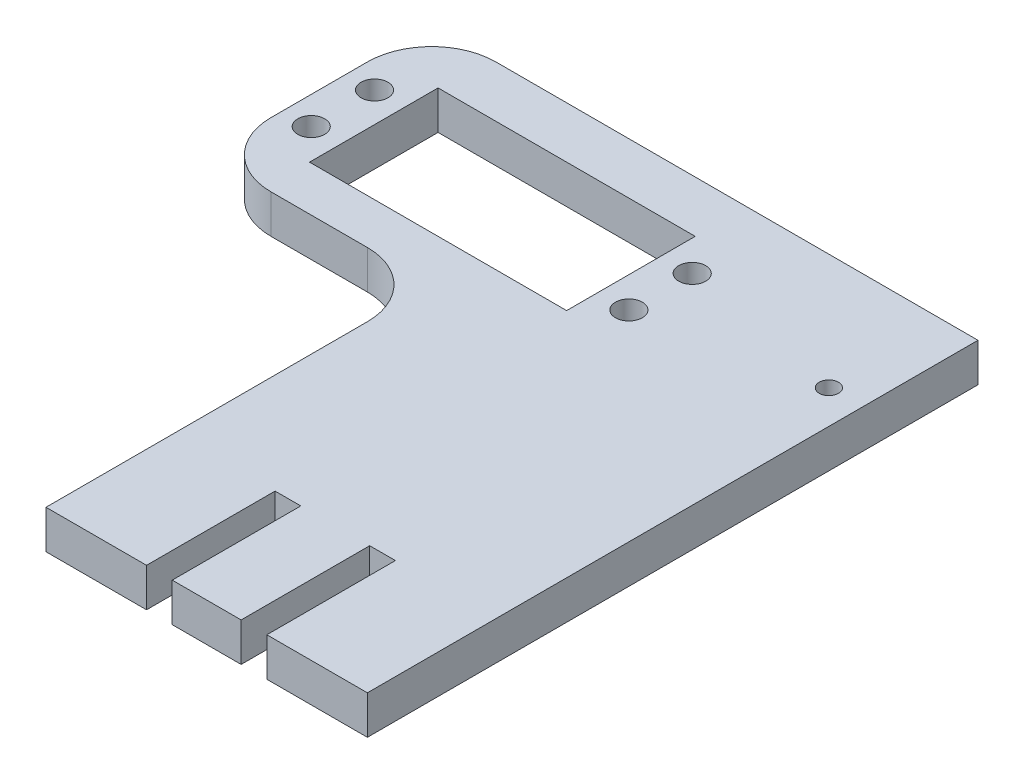
SolidWorks part; units mm, degrees
ref_plane "Front Plane" through (0, 0, 0) normal (0, 0, 1) x (1, 0, 0)
ref_plane "Top Plane" through (0, 0, 0) normal (0, 1, 0) x (1, 0, 0)
ref_plane "Right Plane" through (0, 0, 0) normal (1, 0, 0) x (0, 0, -1)
sketch "Sketch1" plane through (0, 0, 0) normal (0, 1, 0) x (1, 0, 0)
  line L0 (-25, 47.5) -> (-60, 47.5)
  line L1 (-25, -47.5) -> (25, -47.5)
  line L2 (-25, -47.5) -> (-25, 47.5)
  line L3 (-25, 47.5) -> (25, 47.5)
  line L4 (25, -47.5) -> (25, 47.5)
  line L5 (-25, -47.5) -> (25, 47.5) construction
  line L6 (-25, 47.5) -> (25, -47.5) construction
  line L7 (-60, 47.5) -> (-60, 12.5)
  line L8 (-60, 12.5) -> (-25, 12.5)
  line L9 (-25, 12.5) -> (-25, 47.5)
  point P0 (0, 0)
  dimension "D1" = 50
  dimension "D2" = 95
  dimension "D3" = 35
  dimension "D4" = 35
extrude "Boss-Extrude1" add sketch "Sketch1" along normal blind 6 contours L7 L8 L2 L0 | L1 L4 L3 L2
fillet "Fillet1" radius 10 3 edges at (-25, 3, -12.5) (-60, 3, -47.5) (-60, 3, -12.5)
sketch "Sketch2" plane through (0, 6, 0) normal (0, 1, 0) x (1, 0, 0)
  line L0 (0, -47.5) -> (0, 47.5) construction
  line L1 (-25, -47.5) -> (25, -47.5) construction
  line L2 (25, 47.5) -> (-50, 47.5) construction
  line L3 (-25, -22.5) -> (25, -22.5) construction
  line L4 (-25, -47.5) -> (-25, 2.5) construction
  line L5 (25, -47.5) -> (25, 47.5) construction
  line L6 (-5.36, -47.5) -> (-5.36, -27.5)
  line L7 (-5.36, -27.5) -> (-9.36, -27.5)
  line L8 (-9.36, -27.5) -> (-9.36, -47.5)
  line L9 (-9.36, -47.5) -> (-5.36, -47.5)
  line L10 (9.36, -27.5) -> (9.36, -47.5)
  line L11 (5.36, -27.5) -> (9.36, -27.5)
  line L12 (5.36, -47.5) -> (5.36, -27.5)
  line L13 (9.36, -47.5) -> (5.36, -47.5)
  dimension "D1" = 4
  dimension "D2" = 20
  dimension "D3" = 9.36
extrude "Cut-Extrude1" cut sketch "Sketch2" against normal blind 10
sketch "Sketch3" plane through (0, 6, 0) normal (0, 1, 0) x (1, 0, 0)
  line L0 (-60, 37.5) -> (-60, 22.5) construction
  line L2 (25, 47.5) -> (-50, 47.5) construction
  line L3 (-51, 19.5) -> (-11, 19.5)
  line L4 (-51, 19.5) -> (-51, 39.5)
  line L5 (-51, 39.5) -> (-11, 39.5)
  line L6 (-11, 19.5) -> (-11, 39.5)
  line L7 (-51, 19.5) -> (-11, 39.5) construction
  line L8 (-51, 39.5) -> (-11, 19.5) construction
  point P4 (-31, 29.5)
  dimension "D1" = 9
  dimension "D2" = 20
  dimension "D3" = 40
  dimension "D4" = 8
extrude "Cut-Extrude2" cut sketch "Sketch3" against normal through all
sketch "Sketch4" plane through (0, 0, 0) normal (0, -1, 0) x (-1, 0, 0)
  line L0 (11, 29.5) -> (-25, 29.5) construction
  line L1 (11, 19.5) -> (11, 39.5) construction
  line L2 (-25, -47.5) -> (-25, 47.5) construction
  circle A0 centre (-19.8, 29.5) radius 1.5
  dimension "D1" = 5.2
  dimension "D2" = 3
extrude "Cut-Extrude3" cut sketch "Sketch4" against normal through all
sketch "Sketch5" plane through (0, 6, 0) normal (0, 1, 0) x (1, 0, 0)
  circle A0 centre (-55.6611, 24.425) radius 2.1
  circle A1 centre (-55.6611, 34.275) radius 2.1
  circle A2 centre (-6.2389, 34.275) radius 2.1
  circle A3 centre (-6.2389, 24.425) radius 2.1
  dimension "D1" = 4.2
  dimension "D2" = 4.2
  dimension "D3" = 4.2
  dimension "D4" = 4.2
extrude "Cut-Extrude4" cut sketch "Sketch5" against normal through all
